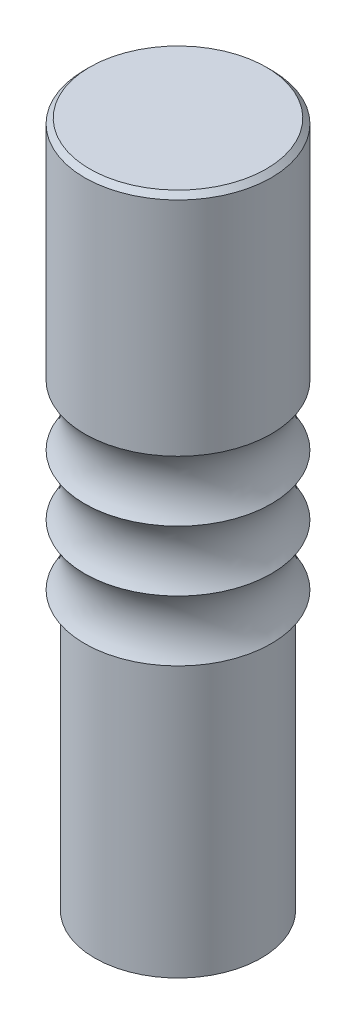
SolidWorks part; units mm, degrees
ref_plane "Plan de face" through (0, 0, 0) normal (0, 0, 1) x (1, 0, 0)
ref_plane "Plan de dessus" through (0, 0, 0) normal (0, 1, 0) x (1, 0, 0)
ref_plane "Plan de droite" through (0, 0, 0) normal (1, 0, 0) x (0, 0, -1)
sketch "Esquisse1" plane through (0, 0, 0) normal (0, 1, 0) x (1, 0, 0)
  circle A0 centre (0, 0) radius 16.5
  dimension "D1" = 33
extrude "Boss.-Extru.1" add sketch "Esquisse1" along normal blind 55 contours A0
sketch "Esquisse4" plane through (0, 55, 0) normal (0, 1, 0) x (1, 0, 0)
  circle A0 centre (0, 0) radius 18.5
  dimension "D1" = 37
sketch "Esquisse5" plane through (0, 0, 0) normal (0, 0, 1) x (1, 0, 0)
  line L0 (0, 55) -> (18.5, 55)
  line L1 (18.5, 55) -> (-18.5, 55) construction
  line L2 (18.5, 136) -> (18.5, 91)
  line L3 (18.5, 136) -> (0, 136)
  line L4 (0, 136) -> (0, 55) construction
  line L5 (0, 55) -> (0, 136)
  arc A0 (18.5, 55) -> (18.5, 67) centre (26.5, 61) cw
  arc A1 (18.5, 67) -> (18.5, 79) centre (26.5, 73) cw
  arc A2 (18.5, 79) -> (18.5, 91) centre (26.5, 85) cw
  dimension "D1" = 12
  dimension "D3" = 12
  dimension "D5" = 12
  dimension "D7" = 81
revolve "Révolution1" add sketch "Esquisse5" angle 360 about L4
chamfer "Chanfrein1" distance 1 angle 45 1 edges at (-18.5, 136, 0)
